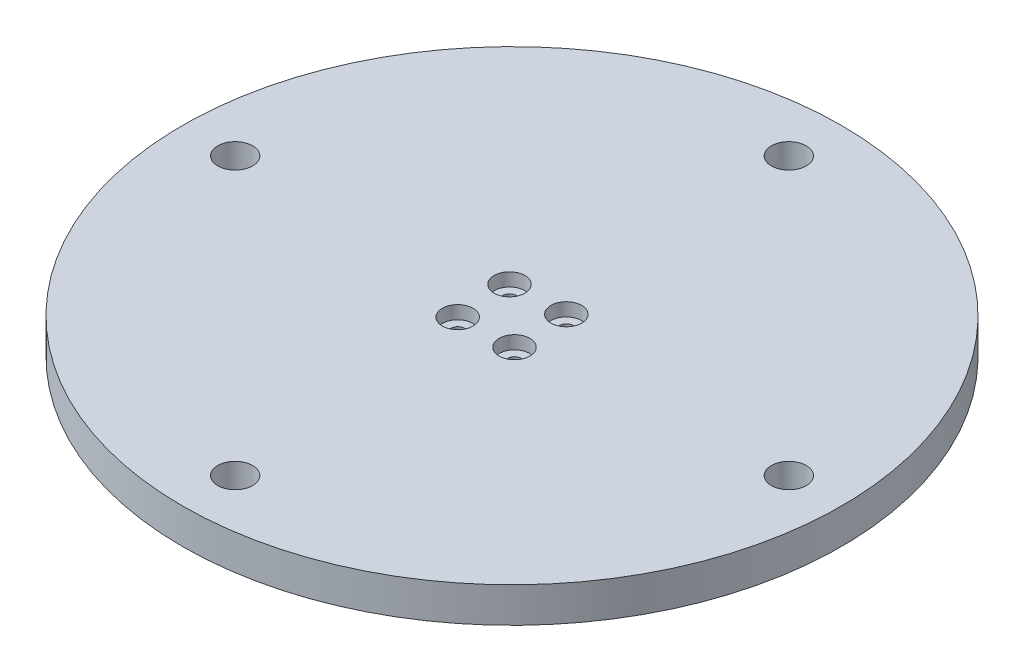
SolidWorks part; units mm, degrees
ref_plane "Alzado" through (0, 0, 0) normal (0, 0, 1) x (1, 0, 0)
ref_plane "Planta" through (0, 0, 0) normal (0, 1, 0) x (1, 0, 0)
ref_plane "Vista lateral" through (0, 0, 0) normal (1, 0, 0) x (0, 0, -1)
sketch "Croquis1" plane through (0, 0, 0) normal (0, 1, 0) x (1, 0, 0)
  circle A0 centre (0, 0) radius 15
extrude "Extruir-Lámina1" add sketch "Croquis1" along normal blind 18 thin thin type one direction reverse wall 2
sketch "Croquis2" plane through (0, 18, 0) normal (0, 1, 0) x (1, 0, 0)
  circle A0 centre (0, 0) radius 75
extrude "Saliente-Extruir1" add sketch "Croquis2" along normal blind 8
sketch "Croquis3" plane through (0, 26, 0) normal (0, 1, 0) x (1, 0, 0)
  line L0 (2.8872, -9.8739) -> (10.0969, -1.9704) construction
  circle A0 centre (5.8969, 6.4644) radius 1.59
  circle A1 centre (-5.8969, -6.4644) radius 1.59
  circle A2 centre (6.4921, -5.9222) radius 1.59
  circle A3 centre (-6.4644, 5.8969) radius 1.5875
  dimension "D1" = 3.175
  dimension "D2" = 3.18
  dimension "D3" = 3.18
  dimension "D4" = 3.18
extrude "Cortar-Extruir1" cut sketch "Croquis3" against normal blind 10
sketch "Croquis5" plane through (0, 18, 0) normal (0, -1, 0) x (1, 0, 0)
  line L0 (0, -75) -> (0, -63)
  circle A0 centre (0, 0) radius 75 construction
  circle A1 centre (0, -63) radius 3.969
  circle A2 centre (-63, 0) radius 3.969
  circle A3 centre (0, 63) radius 3.969
  circle A4 centre (63, 0) radius 3.969
  point P16 (0, 0)
  dimension "D1" = 7.938
  dimension "D2" = 4
extrude "Cortar-Extruir2" cut sketch "Croquis5" against normal blind 10
sketch "Croquis6" plane through (0, 26, 0) normal (0, 1, 0) x (1, 0, 0)
  circle A0 centre (5.8969, 6.4644) radius 3.5
  circle A1 centre (-6.4644, 5.8969) radius 3.5
  circle A2 centre (-5.8969, -6.4644) radius 3.5
  circle A3 centre (6.4921, -5.9222) radius 3.5
extrude "Cortar-Extruir3" cut sketch "Croquis6" against normal blind 3
